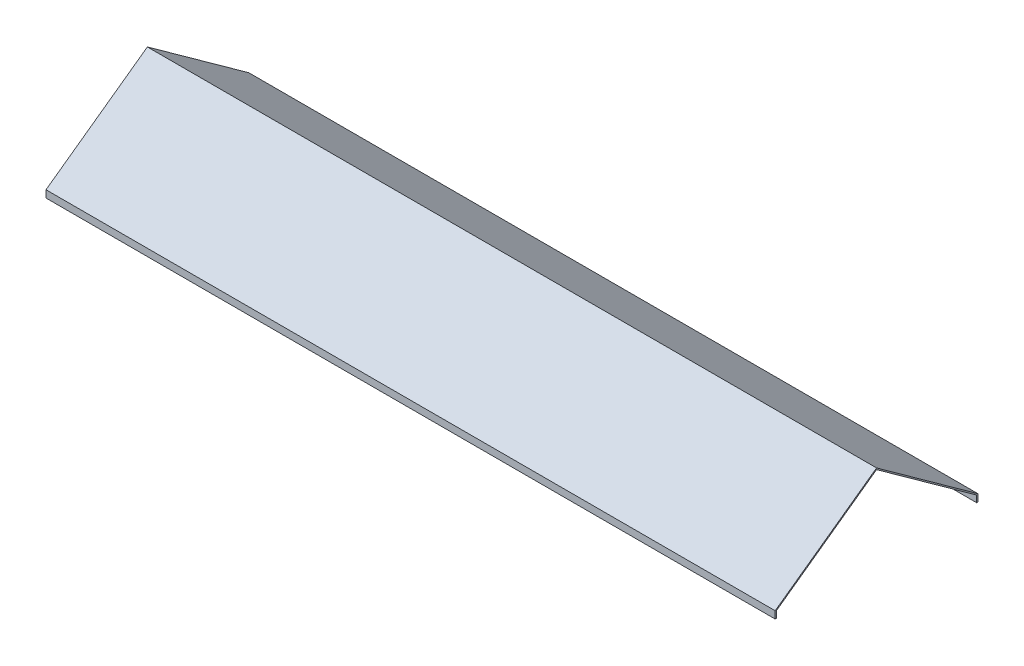
SolidWorks part; units mm, degrees
ref_plane "Front Plane" through (0, 0, 0) normal (0, 0, 1) x (1, 0, 0)
ref_plane "Top Plane" through (0, 0, 0) normal (0, 1, 0) x (1, 0, 0)
ref_plane "Right Plane" through (0, 0, 0) normal (1, 0, 0) x (0, 0, -1)
sketch "Sketch1" plane through (0, 0, 0) normal (1, 0, 0) x (0, 0, -1)
  line L0 (0, 0) -> (0, 90) construction
  line L1 (0, 0) -> (-125, 0) construction
  line L2 (0, 0) -> (125, 0) construction
  line L3 (-125, 0) -> (0, 90)
  line L4 (0, 90) -> (125, 0)
  line L5 (-125, 0) -> (-125, -8.2316)
  line L6 (-125, -8.2316) -> (-126.5, -8.2316)
  line L7 (-126.5, -8.2316) -> (-126.5, 0.7684)
  line L8 (-126.5, 0.7684) -> (0, 91.8484)
  line L9 (0, 91.8484) -> (126.5995, 0.6967)
  line L10 (126.5995, 0.6967) -> (126.5995, -8.3033)
  line L11 (126.5995, -8.3033) -> (125, -8.3033)
  line L12 (125, -8.3033) -> (125, 0)
  dimension "D1" = 90
  dimension "D2" = 125
  dimension "D3" = 125
  dimension "D4" = 1.5
  dimension "D5" = 1.5
  dimension "D6" = 1.5
  dimension "D7" = 9
  dimension "D8" = 9
extrude "Boss-Extrude1" add sketch "Sketch1" along normal blind 910
